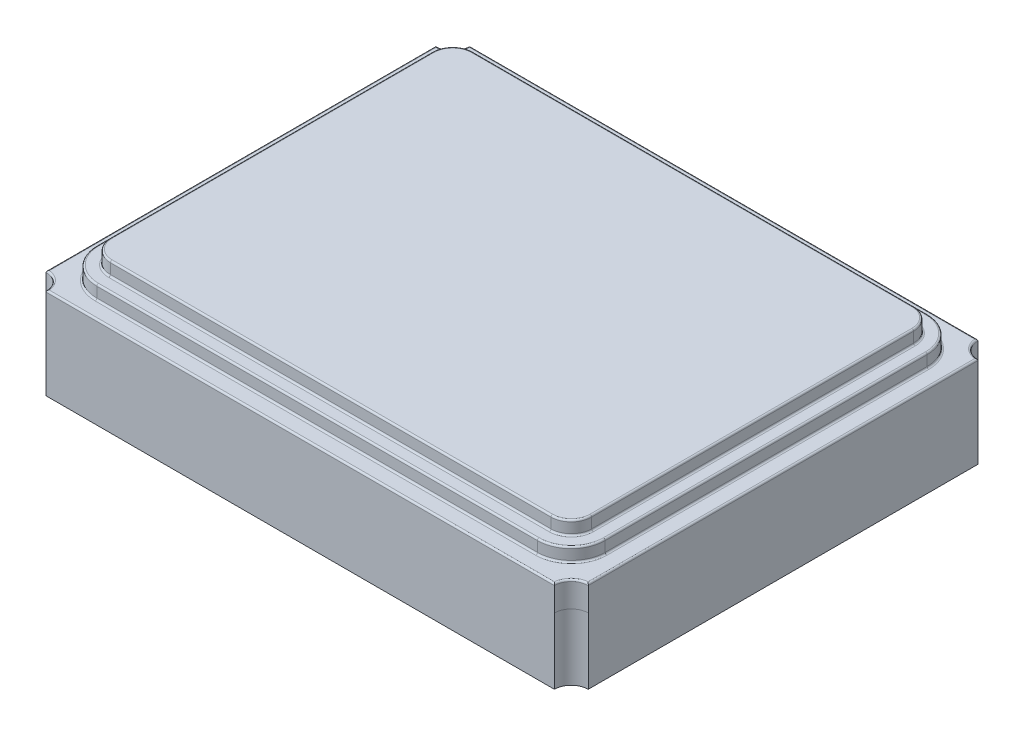
SolidWorks part; units mm, degrees
ref_plane "Front Plane" through (0, 0, 0) normal (0, 0, 1) x (1, 0, 0)
ref_plane "Top Plane" through (0, 0, 0) normal (0, 1, 0) x (1, 0, 0)
ref_plane "Right Plane" through (0, 0, 0) normal (1, 0, 0) x (0, 0, -1)
sketch "Sketch1" plane through (0, 0, 0) normal (0, 1, 0) x (1, 0, 0)
  line L0 (1.6, -1.25) -> (-1.6, 1.25) construction
  line L1 (-1.5, 1.25) -> (1.5, 1.25)
  line L2 (-1.6, 1.15) -> (-1.6, -1.15)
  line L3 (-1.5, -1.25) -> (1.5, -1.25)
  line L4 (1.6, 1.15) -> (1.6, -1.15)
  line L5 (1.6, 1.25) -> (1.5, 1.25) construction
  line L6 (1.6, 1.25) -> (1.6, 1.15) construction
  line L7 (-1.5, 1.25) -> (-1.6, 1.25) construction
  line L8 (-1.6, 1.25) -> (-1.6, 1.15) construction
  line L9 (-1.6, 1.15) -> (-1.6, 1.25) construction
  line L10 (-1.6, -1.25) -> (-1.5, -1.25) construction
  arc A0 (1.5, 1.25) -> (1.6, 1.15) centre (1.6, 1.25) ccw
  arc A1 (1.6, -1.15) -> (1.5, -1.25) centre (1.6, -1.25) ccw
  arc A2 (-1.5, -1.25) -> (-1.6, -1.15) centre (-1.6, -1.25) ccw
  arc A3 (-1.6, 1.15) -> (-1.5, 1.25) centre (-1.6, 1.25) ccw
  dimension "D3" = 0.2
  dimension "D1" = 3.2
  dimension "D2" = 2.5
  dimension "D4" = 2.3
  dimension "D5" = 3
extrude "Boss-Extrude1" add sketch "Sketch1" along normal blind 0.54
sketch "Sketch2" plane through (0, 0.54, 0) normal (0, 1, 0) x (1, 0, 0)
  line L0 (1.5, -1.15) -> (-1.5, 1.15) construction
  line L1 (-1.3, 1.15) -> (1.3, 1.15)
  line L2 (-1.5, 0.95) -> (-1.5, -0.95)
  line L3 (-1.3, -1.15) -> (1.3, -1.15)
  line L4 (1.5, 0.95) -> (1.5, -0.95)
  line L5 (1.5, 1.25) -> (-1.5, 1.25) construction
  line L6 (-1.6, 1.15) -> (-1.6, -1.15) construction
  arc A0 (1.5, -0.95) -> (1.3, -1.15) centre (1.3, -0.95) cw
  arc A1 (-1.3, -1.15) -> (-1.5, -0.95) centre (-1.3, -0.95) cw
  arc A2 (-1.5, 0.95) -> (-1.3, 1.15) centre (-1.3, 0.95) cw
  arc A3 (1.5, 0.95) -> (1.3, 1.15) centre (1.3, 0.95) ccw
  dimension "D3" = 0.2
  dimension "D1" = 0.1
  dimension "D2" = 0.1
extrude "Boss-Extrude2" add sketch "Sketch2" along normal blind 0.08
sketch "Sketch4" plane through (0, 0.62, 0) normal (0, 1, 0) x (1, 0, 0)
  line L12 (1.42, -0.95) -> (1.42, 0.95)
  line L13 (1.3, 1.07) -> (-1.3, 1.07)
  line L14 (-1.42, 0.95) -> (-1.42, -0.95)
  line L15 (-1.3, -1.07) -> (1.3, -1.07)
  line L16 (1.42, -0.95) -> (1.42, 0.95)
  line L17 (1.3, 1.07) -> (-1.3, 1.07)
  line L18 (-1.42, 0.95) -> (-1.42, -0.95)
  line L19 (-1.3, -1.07) -> (1.3, -1.07)
  arc A12 (1.3, -1.07) -> (1.42, -0.95) centre (1.3, -0.95) ccw
  arc A13 (1.42, 0.95) -> (1.3, 1.07) centre (1.3, 0.95) ccw
  arc A14 (-1.3, 1.07) -> (-1.42, 0.95) centre (-1.3, 0.95) ccw
  arc A15 (-1.42, -0.95) -> (-1.3, -1.07) centre (-1.3, -0.95) ccw
  arc A16 (1.3, -1.07) -> (1.42, -0.95) centre (1.3, -0.95) ccw
  arc A17 (1.42, 0.95) -> (1.3, 1.07) centre (1.3, 0.95) ccw
  arc A18 (-1.3, 1.07) -> (-1.42, 0.95) centre (-1.3, 0.95) ccw
  arc A19 (-1.42, -0.95) -> (-1.3, -1.07) centre (-1.3, -0.95) ccw
  dimension "D1" = 0.08
extrude "Boss-Extrude3" add sketch "Sketch4" along normal blind 0.08
sketch "Sketch5" plane through (0, 0, 0) normal (0, -1, 0) x (1, 0, 0)
  line L0 (-1.43, 1.25) -> (-1.5, 1.25)
  line L1 (-1.6, 1.15) -> (-1.6, 1.08)
  line L2 (-1.4451, 1.18) -> (-0.6, 1.18)
  line L3 (-0.6, 1.18) -> (-0.6, 0.65)
  line L4 (-0.6, 0.65) -> (-0.9, 0.35)
  line L5 (-0.9, 0.35) -> (-1.53, 0.35)
  line L6 (-1.53, 0.35) -> (-1.53, 1.0951)
  line L7 (-1.6, -1.15) -> (-1.6, 1.15) construction
  line L8 (-1.5, 1.25) -> (1.5, 1.25) construction
  line L9 (0, 0) -> (0, -0.4357) construction
  line L10 (0, 0) -> (0.4719, 0) construction
  line L11 (1.53, 0.35) -> (1.53, 1.0951)
  line L12 (-1.53, -0.35) -> (-0.6, -0.35)
  line L13 (-0.6, -0.35) -> (-0.6, -1.18)
  line L14 (1.53, 0.35) -> (0.6, 0.35)
  line L15 (1.4451, 1.18) -> (0.6, 1.18)
  line L16 (1.6, 1.15) -> (1.6, 1.08)
  line L17 (1.43, 1.25) -> (1.5, 1.25)
  line L18 (1.43, -1.25) -> (1.5, -1.25)
  line L19 (1.6, -1.15) -> (1.6, -1.08)
  line L20 (1.4451, -1.18) -> (0.6, -1.18)
  line L21 (0.6, -1.18) -> (0.6, -0.35)
  line L22 (0.6, 0.35) -> (0.6, 1.18)
  line L23 (0.6, -0.35) -> (1.53, -0.35)
  line L24 (1.53, -0.35) -> (1.53, -1.0951)
  line L25 (-1.53, -0.35) -> (-1.53, -1.0951)
  line L29 (-1.4451, -1.18) -> (-0.6, -1.18)
  line L30 (-1.6, -1.15) -> (-1.6, -1.08)
  line L31 (-1.43, -1.25) -> (-1.5, -1.25)
  arc A0 (-1.6, 1.08) -> (-1.53, 1.0951) centre (-1.6, 1.25) ccw
  arc A1 (-1.6, 1.15) -> (-1.5, 1.25) centre (-1.6, 1.25) ccw
  arc A2 (-1.6, 1.15) -> (-1.5, 1.25) centre (-1.6, 1.25) ccw construction
  arc A3 (-1.4451, 1.18) -> (-1.43, 1.25) centre (-1.6, 1.25) ccw
  arc A4 (1.4451, 1.18) -> (1.43, 1.25) centre (1.6, 1.25) cw
  arc A5 (1.6, 1.15) -> (1.5, 1.25) centre (1.6, 1.25) cw
  arc A6 (1.6, 1.08) -> (1.53, 1.0951) centre (1.6, 1.25) cw
  arc A7 (1.6, -1.08) -> (1.53, -1.0951) centre (1.6, -1.25) ccw
  arc A8 (1.6, -1.15) -> (1.5, -1.25) centre (1.6, -1.25) ccw
  arc A9 (1.4451, -1.18) -> (1.43, -1.25) centre (1.6, -1.25) ccw
  arc A10 (-1.4451, -1.18) -> (-1.43, -1.25) centre (-1.6, -1.25) cw
  arc A11 (-1.6, -1.15) -> (-1.5, -1.25) centre (-1.6, -1.25) cw
  arc A12 (-1.6, -1.08) -> (-1.53, -1.0951) centre (-1.6, -1.25) cw
  dimension "D7" = 0.07
  dimension "D1" = 0.6
  dimension "D2" = 0.35
  dimension "D3" = 45
  dimension "D4" = 0.3
  dimension "D5" = 0.07
  dimension "D6" = 0.07
split line "Split Line1"
sketch "Sketch6" plane through (0, 0, 1.25) normal (0, 0, 1) x (1, 0, 0)
  line L0 (1.6, 0.54) -> (1.6, 0) construction
  line L1 (1.5, 0.54) -> (1.6, 0.54)
  line L2 (1.5, 0.54) -> (1.5, 0.39)
  line L3 (1.5, 0.39) -> (1.6, 0.39)
  line L4 (1.6, 0.54) -> (1.6, 0.39)
  line L5 (-1.6, 0.54) -> (-1.6, 0) construction
  line L6 (-1.5, 0.54) -> (-1.6, 0.54)
  line L7 (-1.5, 0.54) -> (-1.5, 0.39)
  line L8 (-1.5, 0.39) -> (-1.6, 0.39)
  line L9 (-1.6, 0.54) -> (-1.6, 0.39)
  dimension "D1" = 0.15
split line "Split Line2"
sketch "Sketch7" plane through (0, 0, -1.25) normal (0, 0, -1) x (-1, 0, 0)
  line L0 (1.6, 0.54) -> (1.6, 0) construction
  line L1 (1.5, 0.54) -> (1.6, 0.54)
  line L2 (1.5, 0.54) -> (1.5, 0.39)
  line L3 (1.5, 0.39) -> (1.6, 0.39)
  line L4 (1.6, 0.54) -> (1.6, 0.39)
  line L5 (-1.6, 0.54) -> (-1.6, 0) construction
  line L6 (-1.5, 0.54) -> (-1.6, 0.54)
  line L7 (-1.5, 0.54) -> (-1.5, 0.39)
  line L8 (-1.5, 0.39) -> (-1.6, 0.39)
  line L9 (-1.6, 0.54) -> (-1.6, 0.39)
  dimension "D1" = 0.15
split line "Split Line3"
fillet "Fillet1" radius 0.01 40 edges at (0, 0.7, 1.07) (-1.3849, 0.7, 1.0349) (-1.42, 0.7, 0) (-1.3849, 0.7, -1.0349) (0, 0.7, -1.07) (1.3849, 0.7, -1.0349) (1.42, 0.7, 0) (1.3849, 0.7, 1.0349) (1.42, 0.62, 0) (1.3849, 0.62, -1.0349) (0, 0.62, -1.07) (-1.3849, 0.62, -1.0349) (-1.42, 0.62, 0) (-1.3849, 0.62, 1.0349) (0, 0.62, 1.07) (1.3849, 0.62, 1.0349) (0, 0.62, 1.15) (-1.4414, 0.62, 1.0914) (-1.5, 0.62, 0) (-1.4414, 0.62, -1.0914) (0, 0.62, -1.15) (1.4414, 0.62, -1.0914) (1.5, 0.62, 0) (1.4414, 0.62, 1.0914) (1.4414, 0.54, -1.0914) (0, 0.54, -1.15) (-1.4414, 0.54, -1.0914) (-1.5, 0.54, 0) (-1.4414, 0.54, 1.0914) (0, 0.54, 1.15) (1.4414, 0.54, 1.0914) (1.5, 0.54, 0) (0, 0.54, 1.25) (-1.5293, 0.54, 1.1793) (-1.6, 0.54, 0) (-1.5293, 0.54, -1.1793) (0, 0.54, -1.25) (1.5293, 0.54, -1.1793) (1.6, 0.54, 0) (1.5293, 0.54, 1.1793)
